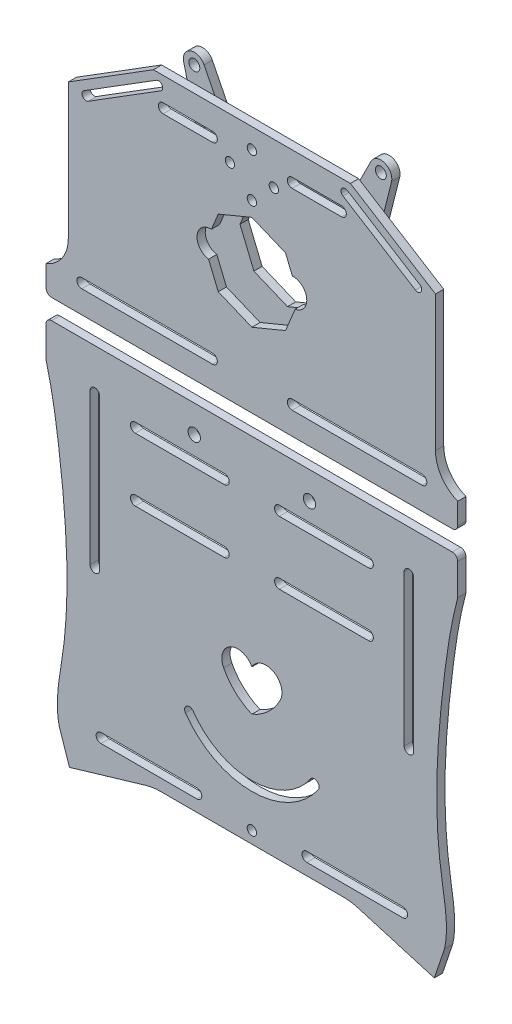
SolidWorks part; units mm, degrees
ref_plane "前视基准面" through (0, 0, 0) normal (0, 0, 1) x (1, 0, 0)
ref_plane "上视基准面" through (0, 0, 0) normal (0, 1, 0) x (1, 0, 0)
ref_plane "右视基准面" through (0, 0, 0) normal (1, 0, 0) x (0, 0, -1)
sketch "草图1" plane through (0, 0, 0) normal (0, 0, 1) x (1, 0, 0)
  line L0 (0, 148.5) -> (0, -94.9538) construction
  line L1 (105, -148.5) -> (-105, -148.5) construction
  line L2 (105, -148.5) -> (105, 148.5) construction
  line L3 (105, 148.5) -> (-105, 148.5) construction
  line L4 (-105, -148.5) -> (-105, 148.5) construction
  line L5 (105, -148.5) -> (-105, 148.5) construction
  line L6 (105, 148.5) -> (-105, -148.5) construction
  line L7 (35.8892, 121.6645) -> (-35.8892, 121.6645)
  line L8 (-35.8892, 121.6645) -> (-66.9017, 102.292)
  line L9 (-75, 40.9339) -> (-75, 31.2613)
  line L10 (-66.9017, 102.292) -> (-66.9017, 52.8701)
  line L11 (75, 40.9339) -> (75, 31.2613)
  line L12 (66.9017, 102.292) -> (66.9017, 52.8701)
  line L13 (35.8892, 121.6645) -> (66.9017, 102.292)
  line L14 (-75, 31.2613) -> (75, 31.2613)
  line L15 (-60, -148.5) -> (-60, -91.8129)
  line L16 (-75, 23.94) -> (75, 23.94)
  line L17 (-75, 23.94) -> (-75, 10.5626)
  line L18 (-38.8455, -105.5906) -> (-66.4608, -113.7617)
  line L19 (-66.4608, -113.7617) -> (-70.1743, -102.7328)
  line L20 (75, 23.94) -> (75, 10.5626)
  line L21 (66.4608, -113.7617) -> (70.1743, -102.7328)
  line L22 (38.8455, -105.5906) -> (66.4608, -113.7617)
  line L23 (-105, 93.0519) -> (105, 93.0519)
  line L24 (-105, 63.0519) -> (105, 63.0519)
  line L25 (-105, -90.0629) -> (-70.5337, -90.0629)
  line L26 (-105, -60.0629) -> (-67.4027, -60.0629)
  line L27 (60, -148.5) -> (60, 148.5)
  line L28 (-60, -58.3129) -> (-45, -58.3129)
  line L29 (-60, -61.8129) -> (-45, -61.8129)
  line L30 (-36, -58.3129) -> (-21, -58.3129)
  line L31 (-36, -61.8129) -> (-21, -61.8129)
  line L32 (-60, -88.3129) -> (-45, -88.3129)
  line L33 (-60, -91.8129) -> (-45, -91.8129)
  line L34 (-36, -88.3129) -> (-21, -88.3129)
  line L35 (-36, -91.8129) -> (-21, -91.8129)
  line L36 (-60, -58.3129) -> (-60, 148.5)
  line L37 (-19.25, -90.0629) -> (105, -90.0629)
  line L38 (-19.25, -60.0629) -> (19.25, -60.0629)
  line L39 (-60, -88.3129) -> (-60, -61.8129)
  line L40 (21, -58.3129) -> (36, -58.3129)
  line L41 (45, -58.3129) -> (60, -58.3129)
  line L42 (60, -61.8129) -> (45, -61.8129)
  line L43 (36, -61.8129) -> (21, -61.8129)
  line L44 (21, -88.3129) -> (36, -88.3129)
  line L45 (21, -91.8129) -> (36, -91.8129)
  line L46 (45, -88.3129) -> (60, -88.3129)
  line L47 (45, -91.8129) -> (60, -91.8129)
  line L48 (37.75, -60.0629) -> (43.25, -60.0629)
  line L49 (58.25, -60.0629) -> (105, -60.0629)
  line L50 (-60, 94.8019) -> (-45, 94.8019)
  line L51 (-36, 94.8019) -> (-21, 94.8019)
  line L52 (-60, 91.3019) -> (-45, 91.3019)
  line L53 (-36, 91.3019) -> (-21, 91.3019)
  line L54 (-60, 64.8019) -> (-45, 64.8019)
  line L55 (-60, 61.3019) -> (-45, 61.3019)
  line L56 (-36, 64.8019) -> (-21, 64.8019)
  line L57 (-36, 61.3019) -> (-21, 61.3019)
  line L58 (21, 94.8019) -> (36, 94.8019)
  line L59 (21, 91.3019) -> (36, 91.3019)
  line L60 (45, 94.8019) -> (60, 94.8019)
  line L61 (45, 91.3019) -> (60, 91.3019)
  line L62 (21, 61.3019) -> (36, 61.3019)
  line L63 (21, 64.8019) -> (36, 64.8019)
  line L64 (45, 61.3019) -> (60, 61.3019)
  line L65 (45, 64.8019) -> (60, 64.8019)
  line L66 (-33.1709, -104.7687) -> (33.1709, -104.7687)
  line L67 (0, -104.7687) -> (0, -148.5) construction
  arc A0 (-75, 40.9339) -> (-66.9017, 52.8701) centre (-79.7474, 52.8701) ccw
  arc A1 (75, 40.9339) -> (66.9017, 52.8701) centre (79.7474, 52.8701) cw
  arc A3 (-60, -88.3129) -> (-60, -91.8129) centre (-60, -90.0629) ccw
  arc A4 (-60, -58.3129) -> (-60, -61.8129) centre (-60, -60.0629) ccw
  circle A5 centre (-60, 63.0519) radius 1.75
  circle A6 centre (-60, 93.0519) radius 1.75
  circle A7 centre (60, 93.0519) radius 1.75
  circle A8 centre (60, 63.0519) radius 1.75
  arc A9 (60, -91.8129) -> (60, -88.3129) centre (60, -90.0629) ccw
  arc A10 (60, -61.8129) -> (60, -58.3129) centre (60, -60.0629) ccw
  arc A11 (-36, -58.3129) -> (-36, -61.8129) centre (-36, -60.0629) ccw
  arc A12 (-36, -88.3129) -> (-36, -91.8129) centre (-36, -90.0629) ccw
  arc A13 (36, -61.8129) -> (36, -58.3129) centre (36, -60.0629) ccw
  arc A14 (36, -91.8129) -> (36, -88.3129) centre (36, -90.0629) ccw
  arc A15 (-45, -61.8129) -> (-45, -58.3129) centre (-45, -60.0629) ccw
  arc A16 (-21, -61.8129) -> (-21, -58.3129) centre (-21, -60.0629) ccw
  arc A17 (-45, -91.8129) -> (-45, -88.3129) centre (-45, -90.0629) ccw
  arc A18 (-21, -91.8129) -> (-21, -88.3129) centre (-21, -90.0629) ccw
  arc A19 (45, -58.3129) -> (45, -61.8129) centre (45, -60.0629) ccw
  arc A20 (21, -58.3129) -> (21, -61.8129) centre (21, -60.0629) ccw
  arc A21 (21, -88.3129) -> (21, -91.8129) centre (21, -90.0629) ccw
  arc A22 (45, -88.3129) -> (45, -91.8129) centre (45, -90.0629) ccw
  circle A23 centre (-36, 93.0519) radius 1.75
  circle A24 centre (-36, 63.0519) radius 1.75
  circle A25 centre (36, 93.0519) radius 1.75
  circle A26 centre (36, 63.0519) radius 1.75
  circle A27 centre (-45, 93.0519) radius 1.75
  circle A28 centre (-21, 93.0519) radius 1.75
  circle A29 centre (-45, 63.0519) radius 1.75
  circle A30 centre (-21, 63.0519) radius 1.75
  circle A31 centre (21, 93.0519) radius 1.75
  circle A32 centre (21, 63.0519) radius 1.75
  circle A33 centre (45, 93.0519) radius 1.75
  circle A34 centre (45, 63.0519) radius 1.75
  arc A35 (33.1709, -104.7687) -> (38.8455, -105.5906) centre (33.1709, -124.7687) cw
  arc A36 (-33.1709, -104.7687) -> (-38.8455, -105.5906) centre (-33.1709, -124.7687) ccw
  spline S0 degree 3 poles (-75, 10.5626) (-72.6959, 1.9073) (-70.3396, -13.3728) (-67.1028, -43.6255) (-66.7657, -72.9327) (-71.8903, -95.1489) (-70.1743, -102.7328) knots 0 0 0 0 0.235247 0.406294 0.801186 1 1 1 1
  spline S1 degree 3 poles (75, 10.5626) (72.6959, 1.9073) (70.3396, -13.3728) (67.1028, -43.6255) (66.7657, -72.9327) (71.8903, -95.1489) (70.1743, -102.7328) knots 0 0 0 0 0.235247 0.406294 0.801186 1 1 1 1
  point P0 (0, 0)
  point P27 (0, 121.6645)
  point P42 (0, -94.0966)
  dimension "D1" = 60
  dimension "D4" = 20
  dimension "D5" = 24
  dimension "D7" = 24
  dimension "D9" = 15
  dimension "D10" = 15
  dimension "D13" = 24
  dimension "D17" = 15
  dimension "D2" = 30
  dimension "D3" = 30
  dimension "D6" = 24
  dimension "D8" = 24
  dimension "D11" = 15
  dimension "D12" = 15
  dimension "D14" = 24
  dimension "D15" = 24
  dimension "D16" = 24
  dimension "D18" = 15
  dimension "D19" = 15
  dimension "D20" = 15
  dimension "D21" = 15
  dimension "D22" = 15
  dimension "D23" = 15
  dimension "D24" = 15
  dimension "D25" = 15
  dimension "D26" = 15
  dimension "D27" = 15
  dimension "D28" = 15
  dimension "D29" = 3.5
  dimension "D30" = 3.5
  dimension "D31" = 3.5
extrude "凸台-拉伸1" add sketch "草图1" along normal blind 3
sketch "草图7" plane through (0, 0, 0) normal (0, 0, -1) x (-1, 0, 0)
  line L0 (0, 121.6645) -> (0, -104.7687) construction
  line L1 (-35.8892, 121.6645) -> (35.8892, 121.6645) construction
  line L2 (33.1709, -104.7687) -> (-33.1709, -104.7687) construction
  line L3 (0, 41.2613) -> (-21, 41.2613) construction
  line L4 (0, 41.2613) -> (21, 41.2613) construction
  line L5 (0, 13.94) -> (-21, 13.94) construction
  line L6 (0, 13.94) -> (21, 13.94) construction
  line L7 (75, 23.94) -> (-75, 23.94) construction
  line L8 (75, 31.2613) -> (-75, 31.2613) construction
  circle A0 centre (-21, 41.2613) radius 1.75
  circle A1 centre (21, 41.2613) radius 1.75
  circle A2 centre (-21, 13.94) radius 2.25
  circle A3 centre (21, 13.94) radius 2.25
  dimension "D1" = 10
  dimension "D2" = 10
extrude "切除-拉伸2" cut sketch "草图7" against normal through all
sketch "草图9" plane through (0, 0, 3) normal (0, 0, 1) x (1, 0, 0)
  line L0 (-70.7828, -98.747) -> (70.7828, -98.747) construction
  line L1 (0, -98.747) -> (0, -104.7687) construction
  line L2 (55, -100.497) -> (20, -100.497)
  line L3 (-55, -96.997) -> (-20, -96.997)
  line L4 (-55, -100.497) -> (-20, -100.497)
  line L5 (-33.1709, -104.7687) -> (33.1709, -104.7687) construction
  line L6 (55, -96.997) -> (20, -96.997)
  arc A0 (-55, -96.997) -> (-55, -100.497) centre (-55, -98.747) ccw
  arc A1 (-20, -100.497) -> (-20, -96.997) centre (-20, -98.747) ccw
  arc A2 (20, -100.497) -> (20, -96.997) centre (20, -98.747) cw
  arc A3 (55, -96.997) -> (55, -100.497) centre (55, -98.747) cw
  spline S0 degree 3 poles (-75, 10.5626) (-72.6959, 1.9073) (-70.3396, -13.3728) (-67.1028, -43.6255) (-66.7657, -72.9327) (-71.8903, -95.1489) (-70.1743, -102.7328) knots 0 0 0 0 0.235247 0.406294 0.801186 1 1 1 1 construction
  spline S1 degree 3 poles (75, 10.5626) (72.6959, 1.9073) (70.3396, -13.3728) (67.1028, -43.6255) (66.7657, -72.9327) (71.8903, -95.1489) (70.1743, -102.7328) knots 0 0 0 0 0.235247 0.406294 0.801186 1 1 1 1 construction
  dimension "D1" = 35
  dimension "D2" = 20
extrude "切除-拉伸4" cut sketch "草图9" against normal blind 3
sketch "草图10" plane through (0, 0, 3) normal (0, 0, 1) x (1, 0, 0)
  line L0 (-21, -60.0629) -> (-21, -90.0629) construction
  line L1 (21, -60.0629) -> (21, -90.0629) construction
  line L2 (-21, -75.0629) -> (-17.5, -75.0629) construction
  line L4 (12.5, -80.0629) -> (-12.5, -80.0629)
  line L6 (12.5, -70.0629) -> (-12.5, -70.0629)
  line L11 (17.5, -75.0629) -> (21, -75.0629) construction
  arc A0 (-12.5, -70.0629) -> (-12.5, -80.0629) centre (-12.5, -75.0629) ccw
  arc A1 (12.5, -80.0629) -> (12.5, -70.0629) centre (12.5, -75.0629) ccw
  point P11 (0, -75.0629)
extrude "切除-拉伸5" cut sketch "草图10" against normal blind 3
sketch "草图11" plane through (0, 0, 3) normal (0, 0, 1) x (1, 0, 0)
  line L0 (-21, 93.0519) -> (-21, 63.0519) construction
  line L1 (21, 93.0519) -> (21, 63.0519) construction
  line L2 (-21, 78.0519) -> (-20, 78.0519) construction
  line L4 (15, 73.0519) -> (-15, 73.0519)
  line L6 (15, 83.0519) -> (-15, 83.0519)
  line L10 (20, 78.0519) -> (21, 78.0519) construction
  arc A0 (-15, 83.0519) -> (-15, 73.0519) centre (-15, 78.0519) ccw
  arc A1 (15, 73.0519) -> (15, 83.0519) centre (15, 78.0519) ccw
  point P10 (0, 78.0519)
  dimension "D1" = 30
extrude "切除-拉伸8" cut sketch "草图11" against normal blind 3
sketch "草图12" plane through (0, 0, 3) normal (0, 0, 1) x (1, 0, 0)
  line L0 (0, 121.6645) -> (0, 83.0519) construction
  line L1 (35.8892, 121.6645) -> (-35.8892, 121.6645) construction
  line L2 (15, 83.0519) -> (-15, 83.0519) construction
  circle A0 centre (0, 106.3718) radius 11 construction
  circle A1 centre (0, 106.3718) radius 8 construction
  circle A2 centre (0, 114.3718) radius 1.7
  circle A3 centre (0, 98.3718) radius 1.7
  circle A4 centre (8, 106.3718) radius 1.7
  circle A5 centre (-8, 106.3718) radius 1.7
extrude "切除-拉伸9" cut sketch "草图12" against normal blind 3
sketch "草图13" plane through (0, 0, 3) normal (0, 0, 1) x (1, 0, 0)
  line L0 (0, -104.7687) -> (0, -80.0629) construction
  line L1 (-33.1709, -104.7687) -> (33.1709, -104.7687) construction
  line L2 (-12.5, -80.0629) -> (12.5, -80.0629) construction
  circle A0 centre (0, -92.4158) radius 8 construction
  circle A1 centre (0, -84.4158) radius 1.7
  circle A2 centre (8, -92.4158) radius 1.7
  circle A3 centre (0, -100.4158) radius 1.7
  circle A4 centre (-8, -92.4158) radius 1.7
extrude "切除-拉伸11" cut sketch "草图13" against normal blind 3
sketch "草图14" plane through (0, 0, 3) normal (0, 0, 1) x (1, 0, 0)
  line L0 (0, 23.94) -> (0, -104.7687) construction
  line L1 (-55.4755, 8.9197) -> (-55.4755, -46.0803)
  line L2 (-58.9755, 8.9197) -> (-58.9755, -46.0803)
  line L3 (-75, 23.94) -> (75, 23.94) construction
  line L4 (-33.1709, -104.7687) -> (33.1709, -104.7687) construction
  line L5 (58.9755, 8.9197) -> (58.9755, -46.0803)
  line L6 (55.4755, 8.9197) -> (55.4755, -46.0803)
  arc A0 (-55.4755, 8.9197) -> (-58.9755, 8.9197) centre (-57.2255, 8.9197) ccw
  arc A1 (-58.9755, -46.0803) -> (-55.4755, -46.0803) centre (-57.2255, -46.0803) ccw
  arc A2 (58.9755, -46.0803) -> (55.4755, -46.0803) centre (57.2255, -46.0803) cw
  arc A3 (55.4755, 8.9197) -> (58.9755, 8.9197) centre (57.2255, 8.9197) cw
extrude "切除-拉伸12" cut sketch "草图14" against normal through all
fillet "圆角1" radius 2 2 edges at (75, 31.2613, 1.5) (-75, 31.2613, 1.5)
fillet "圆角2" radius 2 2 edges at (-75, 23.94, 1.5) (75, 23.94, 1.5)
sketch "草图15" plane through (0, 0, 0) normal (0, 0, -1) x (-1, 0, 0)
  line L0 (0, 121.6645) -> (0, 31.2613) construction
  line L1 (-35.8892, 121.6645) -> (35.8892, 121.6645) construction
  line L2 (73, 31.2613) -> (-73, 31.2613) construction
  line L3 (-27.5188, 121.6645) -> (-63.6963, 99.0657) construction
  line L4 (-35.8892, 121.6645) -> (-66.9017, 102.292) construction
  line L5 (-61.1842, 102.4035) -> (-34.7748, 118.9006)
  line L6 (-59.5948, 99.8591) -> (-33.1854, 116.3562)
  line L7 (27.5188, 121.6645) -> (63.6963, 99.0657) construction
  line L8 (59.5948, 99.8591) -> (33.1854, 116.3562)
  line L9 (61.1842, 102.4035) -> (34.7748, 118.9006)
  arc A0 (-61.1842, 102.4035) -> (-59.5948, 99.8591) centre (-60.3895, 101.1313) ccw
  arc A1 (-33.1854, 116.3562) -> (-34.7748, 118.9006) centre (-33.9801, 117.6284) ccw
  arc A2 (33.1854, 116.3562) -> (34.7748, 118.9006) centre (33.9801, 117.6284) cw
  arc A3 (61.1842, 102.4035) -> (59.5948, 99.8591) centre (60.3895, 101.1313) cw
extrude "切除-拉伸13" cut sketch "草图15" against normal through all
sketch "草图16" plane through (0, 0, 0) normal (0, 0, -1) x (-1, 0, 0)
  line L0 (0, 121.6645) -> (0, 31.2613) construction
  line L1 (-35.8892, 121.6645) -> (35.8892, 121.6645) construction
  line L2 (73, 31.2613) -> (-73, 31.2613) construction
  line L3 (-21, 41.2613) -> (-66.71, 41.2613) construction
  line L4 (-62, 43.0113) -> (-32, 43.0113)
  line L5 (-62, 39.5113) -> (-32, 39.5113)
  line L6 (21, 41.2613) -> (66.71, 41.2613) construction
  line L7 (62, 39.5113) -> (32, 39.5113)
  line L8 (62, 43.0113) -> (32, 43.0113)
  line L9 (-75, 40.9339) -> (-75, 33.2613) construction
  arc A0 (-62, 43.0113) -> (-62, 39.5113) centre (-62, 41.2613) ccw
  arc A1 (-32, 39.5113) -> (-32, 43.0113) centre (-32, 41.2613) ccw
  arc A2 (32, 39.5113) -> (32, 43.0113) centre (32, 41.2613) cw
  arc A3 (62, 43.0113) -> (62, 39.5113) centre (62, 41.2613) cw
  dimension "D2" = 13
sketch "草图17" plane through (0, 0, 0) normal (0, 0, -1) x (-1, 0, 0)
  text T0 "Y" font "黑体" height in points 72
extrude "切除-拉伸15" cut sketch "草图17" against normal through all
sketch "草图18" plane through (0, 0, 0) normal (0, 0, -1) x (-1, 0, 0)
  text T0 "H" font "黑体" height in points 72
extrude "切除-拉伸16" cut sketch "草图18" against normal through all
sketch "草图20" plane through (0, 0, 0) normal (0, 0, -1) x (-1, 0, 0)
  line L0 (-66.9017, 102.292) -> (-66.9017, 52.8701) construction
  line L1 (-66.9017, 95.8596) -> (66.9017, 95.8596)
  line L2 (-66.9017, 95.8596) -> (-66.9017, 52.8701)
  line L3 (-66.9017, 52.8701) -> (66.9017, 52.8701)
  line L4 (66.9017, 95.8596) -> (66.9017, 52.8701)
extrude "凸台-拉伸2" add sketch "草图20" against normal blind 3
sketch "草图21" plane through (0, 0, 0) normal (0, 0, -1) x (-1, 0, 0)
  line L1 (-64.7663, -56.4228) -> (64.4409, -56.4228)
  line L2 (-64.7663, -56.4228) -> (-64.7663, -95.2117)
  line L3 (-64.7663, -95.2117) -> (64.4409, -95.2117)
  line L4 (64.4409, -56.4228) -> (64.4409, -95.2117)
extrude "凸台-拉伸3" add sketch "草图21" against normal blind 3
sketch "草图22" plane through (0, 0, 0) normal (0, 0, -1) x (-1, 0, 0)
  line L1 (-46.7188, -3.1128) -> (-25.8503, -3.1128)
  line L2 (-46.7188, -3.1128) -> (-46.7188, -34.3233)
  line L3 (-46.7188, -34.3233) -> (-25.8503, -34.3233)
  line L4 (-25.8503, -3.1128) -> (-25.8503, -34.3233)
  line L5 (28.8143, -3.1128) -> (49.8675, -3.1128)
  line L6 (28.8143, -3.1128) -> (28.8143, -33.2152)
  line L7 (28.8143, -33.2152) -> (49.8675, -33.2152)
  line L8 (49.8675, -3.1128) -> (49.8675, -33.2152)
extrude "凸台-拉伸4" add sketch "草图22" against normal blind 3
sketch "草图24" plane through (0, 0, 0) normal (0, 0, -1) x (-1, 0, 0)
  line L1 (-64.9961, 44.3276) -> (-28.6954, 44.3276)
  line L2 (-64.9961, 44.3276) -> (-64.9961, 38.3743)
  line L3 (-64.9961, 38.3743) -> (-28.6954, 38.3743)
  line L4 (-28.6954, 44.3276) -> (-28.6954, 38.3743)
  line L5 (29.2405, 44.3276) -> (65.8315, 44.3276)
  line L6 (29.2405, 44.3276) -> (29.2405, 38.3743)
  line L7 (29.2405, 38.3743) -> (65.8315, 38.3743)
  line L8 (65.8315, 44.3276) -> (65.8315, 38.3743)
extrude "凸台-拉伸5" add sketch "草图24" against normal blind 3
sketch "草图25" plane through (0, 0, 0) normal (0, 0, -1) x (-1, 0, 0)
  line L0 (-32.6582, 113.0113) -> (-14.6582, 113.0113)
  line L1 (-32.6582, 109.5113) -> (-14.6582, 109.5113)
  line L2 (-21, 41.2613) -> (21, 41.2613)
  line L3 (-0.3165, 111.2613) -> (0, 41.2613) construction
  line L4 (14.3418, 113.0113) -> (32.3418, 113.0113)
  line L5 (32.3418, 41.2613) -> (-32.6582, 41.2613)
  line L6 (32.3418, 41.2613) -> (32.3418, 111.2613)
  line L8 (-32.6582, 41.2613) -> (-32.6582, 111.2613)
  line L9 (32.3418, 41.2613) -> (-32.6582, 111.2613) construction
  line L10 (30.7168, 109.5113) -> (-32.6582, 41.2613) construction
  line L11 (14.3418, 109.5113) -> (32.3418, 109.5113)
  line L12 (32.3418, 76.2613) -> (-32.6582, 76.2613) construction
  line L13 (12.5918, 111.2613) -> (-12.9082, 111.2613)
  line L14 (12.5918, 41.2613) -> (-12.9082, 41.2613)
  line L15 (14.3418, 43.0113) -> (32.3418, 43.0113)
  line L16 (14.3418, 39.5113) -> (32.3418, 39.5113)
  line L17 (-32.6582, 43.0113) -> (-14.6582, 43.0113)
  line L18 (-32.6582, 39.5113) -> (-14.6582, 39.5113)
  circle A0 centre (-32.6582, 111.2613) radius 1.75
  arc A1 (32.3418, 109.5113) -> (32.3418, 113.0113) centre (32.3418, 111.2613) ccw
  arc A2 (-14.6582, 109.5113) -> (-14.6582, 113.0113) centre (-14.6582, 111.2613) ccw
  arc A3 (14.3418, 113.0113) -> (14.3418, 109.5113) centre (14.3418, 111.2613) ccw
  arc A4 (14.3418, 39.5113) -> (14.3418, 43.0113) centre (14.3418, 41.2613) cw
  arc A5 (-14.6582, 43.0113) -> (-14.6582, 39.5113) centre (-14.6582, 41.2613) cw
  arc A6 (32.3418, 43.0113) -> (32.3418, 39.5113) centre (32.3418, 41.2613) cw
  circle A7 centre (-32.6582, 41.2613) radius 1.75
  point P9 (-0.1582, 76.2613)
  dimension "D1" = 18
  dimension "D2" = 18
extrude "切除-拉伸17" cut sketch "草图25" against normal through all
extrude "切除-拉伸19" cut sketch "草图16" against normal through all
sketch "草图26" plane through (0, 0, 0) normal (0, 0, -1) x (-1, 0, 0)
  line L0 (0, 121.6645) -> (0, -104.7687) construction
  line L1 (-35.8892, 121.6645) -> (35.8892, 121.6645) construction
  line L2 (33.1709, -104.7687) -> (-33.1709, -104.7687) construction
  line L4 (15, 71.877) -> (-15, 71.877)
  line L6 (15, 81.877) -> (-15, 81.877)
  arc A0 (-15, 81.877) -> (-15, 71.877) centre (-15, 76.877) ccw
  arc A1 (15, 71.877) -> (15, 81.877) centre (15, 76.877) ccw
  point P6 (0, 76.877)
extrude "切除-拉伸20" cut sketch "草图26" against normal through all
sketch "草图27" plane through (0, 0, 0) normal (0, 0, -1) x (-1, 0, 0)
  line L0 (0, 23.94) -> (0, -104.7687) construction
  line L1 (73, 23.94) -> (-73, 23.94) construction
  line L2 (33.1709, -104.7687) -> (-33.1709, -104.7687) construction
  line L3 (-42.5, -15.81) -> (-10, -15.81)
  line L4 (42.5, -17.56) -> (-42.5, -17.56)
  line L5 (42.5, -17.56) -> (42.5, 5.44)
  line L6 (42.5, 5.44) -> (-42.5, 5.44)
  line L7 (-42.5, -17.56) -> (-42.5, 5.44)
  line L8 (42.5, -17.56) -> (-42.5, 5.44) construction
  line L9 (42.5, 5.44) -> (-42.5, -17.56) construction
  line L10 (-42.5, -19.31) -> (-10, -19.31)
  line L11 (-42.5, 7.19) -> (-10, 7.19)
  line L12 (-42.5, 3.69) -> (-10, 3.69)
  line L13 (10, 7.19) -> (42.5, 7.19)
  line L14 (10, 3.69) -> (42.5, 3.69)
  line L15 (10, -15.81) -> (42.5, -15.81)
  line L16 (10, -19.31) -> (42.5, -19.31)
  circle A0 centre (-42.5, 5.44) radius 1.75
  circle A1 centre (-42.5, -17.56) radius 1.75
  circle A2 centre (42.5, 5.44) radius 1.75
  circle A3 centre (42.5, -17.56) radius 1.75
  circle A4 centre (-10, 5.44) radius 1.75
  circle A5 centre (-10, -17.56) radius 1.75
  circle A6 centre (10, -17.56) radius 1.75
  circle A7 centre (10, 5.44) radius 1.75
  point P6 (0, -6.06)
  dimension "D4" = 10
  dimension "D5" = 10
  dimension "D1" = 30
  dimension "D2" = 85
  dimension "D3" = 23
extrude "切除-拉伸21" cut sketch "草图27" against normal through all contours L6 A0 L7 | L7 A0 L6 | A4 L11 A0 L6 | A4 L6 A0 L12 | L6 A4 | L6 A4 | A7 L6 | A7 L6 | L6 A7 L14 A2 | L13 A7 L6 A2 | A2 L6 L5 | L6 A2 L5 | L7 A1 L4 | L4 A1 L7 | A5 L3 A1 L4 | A5 L4 A1 L10 | L4 A5 | L4 A5 | A6 L4 | A6 L4 | L4 A6 L16 A3 | L15 A6 L4 A3 | L4 A3 L5 | L5 A3 L4
sketch "草图28" plane through (0, 0, 0) normal (0, 0, -1) x (-1, 0, 0)
  line L0 (0, 23.94) -> (0, -104.7687) construction
  line L1 (73, 23.94) -> (-73, 23.94) construction
  line L2 (33.1709, -104.7687) -> (-33.1709, -104.7687) construction
  arc A0 (0, -48.8123) -> (-10.2848, -54.2659) centre (-5.1424, -51.5391) ccw
  arc A1 (-10.2848, -54.2659) -> (0, -63.7557) centre (7.9187, -44.8556) ccw
  arc A2 (10.2848, -54.2659) -> (0, -63.7557) centre (-7.9187, -44.8556) cw
  arc A3 (0, -48.8123) -> (10.2848, -54.2659) centre (5.1424, -51.5391) cw
extrude "切除-拉伸22" cut sketch "草图28" against normal through all
sketch "草图29" plane through (0, 0, 0) normal (0, 0, -1) x (-1, 0, 0)
  line L0 (0, 23.94) -> (0, -104.7687) construction
  line L1 (73, 23.94) -> (-73, 23.94) construction
  line L2 (33.1709, -104.7687) -> (-33.1709, -104.7687) construction
  arc A0 (-21.3687, -73.4908) -> (21.3687, -73.4908) centre (0, -58.7579) ccw
  arc A1 (-24.1996, -75.4426) -> (24.1996, -75.4426) centre (0, -58.7579) ccw
  arc A2 (-21.3687, -73.4908) -> (-24.1996, -75.4426) centre (-22.7842, -74.4667) ccw
  arc A3 (24.1996, -75.4426) -> (21.3687, -73.4908) centre (22.7842, -74.4667) ccw
extrude "切除-拉伸23" cut sketch "草图29" against normal blind 3
ref_plane "基准面1" through (0, 0, -10) normal (0, 0, -1) x (-1, 0, 0)
sketch "草图30" plane through (0, 0, -10) normal (0, 0, -1) x (-1, 0, 0)
  line L0 (0, 121.6645) -> (0, 31.2613) construction
  line L1 (-35.8892, 121.6645) -> (35.8892, 121.6645) construction
  line L2 (73, 31.2613) -> (-73, 31.2613) construction
  line L3 (-37.8597, 116.6547) -> (-32.6504, 95.8988)
  line L4 (29, 51.9629) -> (-29, 51.9629) construction
  line L5 (29, 51.9629) -> (29, 100.9629) construction
  line L6 (29, 100.9629) -> (-29, 100.9629) construction
  line L7 (-29, 51.9629) -> (-29, 100.9629) construction
  line L8 (29, 51.9629) -> (-29, 100.9629) construction
  line L9 (29, 100.9629) -> (-29, 51.9629) construction
  line L10 (20.4918, 46.4629) -> (-20.4918, 46.4629)
  line L11 (32.5, 56.6756) -> (32.5, 94.6816)
  line L12 (20.8285, 106.4629) -> (-20.8285, 106.4629)
  line L13 (-32.5, 56.6756) -> (-32.5, 94.6816)
  line L14 (32.5, 46.4629) -> (-32.5, 106.4629) construction
  line L15 (32.5, 106.4629) -> (-32.5, 46.4629) construction
  line L16 (-30.4033, 119.4191) -> (-25.2994, 109.2246)
  line L17 (30.4033, 119.4191) -> (25.2994, 109.2246)
  line L18 (37.8597, 116.6547) -> (32.6504, 95.8988)
  line L19 (-33.9801, 117.6284) -> (-33.9801, 31.2613) construction
  line L20 (33.9801, 117.6284) -> (33.9801, 31.2613) construction
  line L21 (-12.9082, 41.2613) -> (-63.75, 41.2613) construction
  line L22 (63.75, 41.2613) -> (12.5918, 41.2613) construction
  line L23 (-37.6932, 42.7489) -> (-32.8586, 54.8162)
  line L24 (-31.2672, 38.3219) -> (-23.8829, 45.1372)
  line L25 (31.2672, 38.3219) -> (23.8829, 45.1372)
  line L26 (37.6932, 42.7489) -> (32.8586, 54.8162)
  circle A0 centre (-29, 100.9629) radius 1.75
  circle A1 centre (29, 100.9629) radius 1.75
  circle A2 centre (-29, 51.9629) radius 1.75
  circle A3 centre (29, 51.9629) radius 1.75
  circle A4 centre (-33.9801, 117.6284) radius 2
  arc A5 (-30.4033, 119.4191) -> (-37.8597, 116.6547) centre (-33.9801, 117.6284) ccw
  arc A6 (30.4033, 119.4191) -> (37.8597, 116.6547) centre (33.9801, 117.6284) cw
  circle A7 centre (33.9801, 117.6284) radius 2
  arc A8 (32.6504, 95.8988) -> (32.5, 94.6816) centre (37.5, 94.6816) ccw
  arc A9 (-32.6504, 95.8988) -> (-32.5, 94.6816) centre (-37.5, 94.6816) cw
  arc A10 (20.8285, 106.4629) -> (25.2994, 109.2246) centre (20.8285, 111.4629) ccw
  arc A11 (-25.2994, 109.2246) -> (-20.8285, 106.4629) centre (-20.8285, 111.4629) ccw
  arc A12 (-14.6582, 39.5113) -> (-14.6582, 43.0113) centre (-14.6582, 41.2613) ccw construction
  arc A13 (-62, 43.0113) -> (-62, 39.5113) centre (-62, 41.2613) ccw construction
  arc A14 (62, 39.5113) -> (62, 43.0113) centre (62, 41.2613) ccw construction
  arc A15 (14.3418, 43.0113) -> (14.3418, 39.5113) centre (14.3418, 41.2613) ccw construction
  circle A16 centre (-33.9801, 41.2613) radius 2
  circle A17 centre (33.9801, 41.2613) radius 2
  arc A18 (-37.6932, 42.7489) -> (-31.2672, 38.3219) centre (-33.9801, 41.2613) ccw
  arc A19 (31.2672, 38.3219) -> (37.6932, 42.7489) centre (33.9801, 41.2613) ccw
  arc A20 (32.5, 56.6756) -> (32.8586, 54.8162) centre (37.5, 56.6756) ccw
  arc A21 (20.4918, 46.4629) -> (23.8829, 45.1372) centre (20.4918, 41.4629) cw
  arc A22 (-23.8829, 45.1372) -> (-20.4918, 46.4629) centre (-20.4918, 41.4629) cw
  arc A23 (-32.8586, 54.8162) -> (-32.5, 56.6756) centre (-37.5, 56.6756) ccw
  point P6 (0, 76.4629)
  point P15 (0, 76.4629)
  point P37 (32.5, 95.2995)
  point P40 (-32.5, 95.2995)
  point P43 (23.9169, 106.4629)
  point P46 (-23.9169, 106.4629)
  point P69 (32.5, 55.7113)
  point P80 (22.4465, 46.4629)
  point P83 (-22.4465, 46.4629)
  point P86 (-32.5, 55.7113)
  dimension "D1" = 5
  dimension "D2" = 5
extrude "凸台-拉伸6" add sketch "草图30" along normal blind 3 separate body
sketch "草图31" plane through (0, 0, -13) normal (0, 0, -1) x (-1, 0, 0)
  line L0 (0, 106.5328) -> (0, 46.4629) construction
  line L1 (-20.4918, 46.4629) -> (20.4918, 46.4629) construction
  line L2 (-32.5, 75.6786) -> (32.5, 75.6786) construction
  line L3 (-32.5, 94.6816) -> (-32.5, 56.6756) construction
  line L4 (32.5, 56.6756) -> (32.5, 94.6816) construction
  line L6 (0, 93.0092) -> (-12.2546, 87.9332)
  line L7 (-12.2546, 87.9332) -> (-17.3306, 75.6786)
  line L8 (-17.3306, 75.6786) -> (-12.2546, 63.4241)
  line L9 (-12.2546, 63.4241) -> (0, 58.348)
  line L10 (0, 58.348) -> (12.2546, 63.4241)
  line L11 (12.2546, 63.4241) -> (17.3306, 75.6786)
  line L12 (17.3306, 75.6786) -> (12.2546, 87.9332)
  line L13 (12.2546, 87.9332) -> (0, 93.0092)
  circle A0 centre (0, 75.6786) radius 16.0114 construction
extrude "切除-拉伸24" cut sketch "草图31" against normal through all
